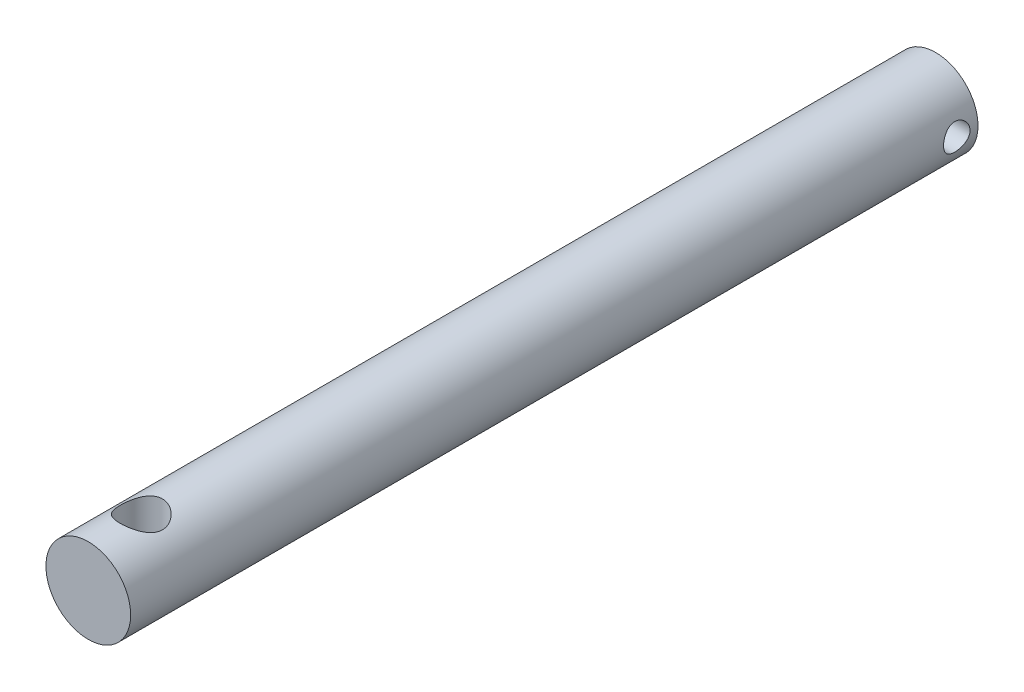
SolidWorks part; units mm, degrees
material "普通碳钢"
ref_plane "前视基准面" through (0, 0, 0) normal (0, 0, 1) x (1, 0, 0)
ref_plane "上视基准面" through (0, 0, 0) normal (0, 1, 0) x (1, 0, 0)
ref_plane "右视基准面" through (0, 0, 0) normal (1, 0, 0) x (0, 0, -1)
sketch "草图1" plane through (0, 0, 0) normal (0, 0, 1) x (1, 0, 0)
  circle A0 centre (0, 0) radius 8
  dimension "D1" = 16
extrude "凸台-拉伸1" add sketch "草图1" along normal blind 160
sketch "草图2" plane through (0, 0, 0) normal (0, 1, 0) x (1, 0, 0)
  line L0 (0, -136.9825) -> (0, -79.026) construction
  line L1 (-8, -160) -> (8, -160) construction
  circle A0 centre (0, -150) radius 4
  dimension "D1" = 8
  dimension "D2" = 10
extrude "切除-拉伸1" cut sketch "草图2" against normal mid plane 20
sketch "草图3" plane through (0, 0, 0) normal (1, 0, 0) x (0, 0, -1)
  line L0 (0, 0) -> (-10.5111, 0) construction
  circle A0 centre (-4, 0) radius 2.5
  dimension "D1" = 5
  dimension "D2" = 4
extrude "切除-拉伸2" cut sketch "草图3" along normal blind 10
